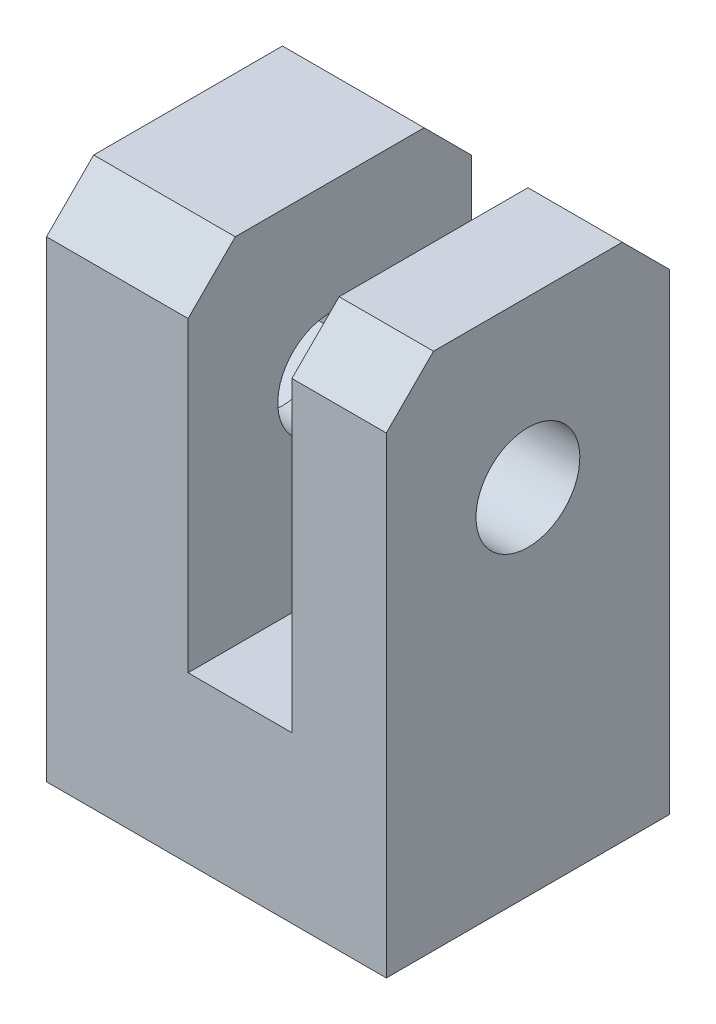
SolidWorks part; units mm, degrees
ref_plane "Front" through (0, 0, 0) normal (0, 0, 1) x (1, 0, 0)
ref_plane "Top" through (0, 0, 0) normal (0, 1, 0) x (1, 0, 0)
ref_plane "Right" through (0, 0, 0) normal (1, 0, 0) x (0, 0, -1)
sketch "Sketch1" plane through (0, 0, 0) normal (0, 0, 1) x (1, 0, 0)
  line L0 (-1.1, 7.5) -> (-1.1, 0)
  line L1 (-2.1, -3.5) -> (3.1, -3.5)
  line L2 (-2.1, -3.5) -> (-2.1, 7.5)
  line L3 (-2.1, 7.5) -> (3.1, 7.5) construction
  line L4 (3.1, -3.5) -> (3.1, 7.5)
  line L7 (-1.1, 0) -> (1.1, 0)
  line L8 (1.1, 0) -> (1.1, 7.5)
  line L10 (-2.1, 7.5) -> (-1.1, 7.5)
  line L11 (1.1, 7.5) -> (3.1, 7.5)
  point P0 (0, 0)
  dimension "D1" = 2
  dimension "D2" = 2.2
  dimension "D3" = 3.5
  dimension "D4" = 7.5
  dimension "D5" = 1
extrude "Boss-Extrude1" add sketch "Sketch1" along normal blind 6
sketch "Sketch2" plane through (1.1, 0, 0) normal (-1, 0, 0) x (0, 0, 1)
  line L0 (3, 4) -> (3, -3.5) construction
  line L2 (6, -3.5) -> (0, -3.5) construction
  circle A0 centre (3, 4) radius 1.1
  dimension "D1" = 2.2
  dimension "D2" = 7.5
extrude "Cut-Extrude1" cut sketch "Sketch2" against normal up to next
sketch "Sketch3" plane through (-1.1, 0, 0) normal (1, 0, 0) x (0, 0, -1)
  circle A0 centre (-3, 4) radius 1.1 construction
  circle A1 centre (-3, 4) radius 1.1
extrude "Cut-Extrude2" cut sketch "Sketch3" against normal up to next
sketch "Sketch5" plane through (-2.1, 0, 0) normal (-1, 0, 0) x (0, 0, 1)
  line L1 (5, 2.8453) -> (5, 5.1547)
  line L2 (5, 5.1547) -> (3, 6.3094)
  line L3 (3, 6.3094) -> (1, 5.1547)
  line L4 (0, 7.5) -> (0, -3.5)
  line L5 (0, -3.5) -> (6, -3.5)
  line L6 (6, -3.5) -> (6, 7.5)
  line L7 (6, 7.5) -> (0, 7.5)
  line L8 (0, 7.5) -> (0, -3.5)
  line L9 (0, -3.5) -> (6, -3.5)
  line L10 (6, -3.5) -> (6, 7.5)
  line L11 (6, 7.5) -> (0, 7.5)
  line L12 (1, 5.1547) -> (1, 2.8453)
  line L13 (1, 2.8453) -> (3, 1.6906)
  line L14 (3, 1.6906) -> (5, 2.8453)
  circle A0 centre (3, 4) radius 2 construction
  dimension "D2" = 4
  dimension "D1" = 0
extrude "Boss-Extrude2" add sketch "Sketch5" along normal blind 2
sketch "Sketch4" plane through (0, -3.5, 0) normal (0, -1, 0) x (1, 0, 0)
  line L0 (0, 0) -> (0, 6) construction
  line L1 (-4.1, 6) -> (3.1, 6) construction
  circle A0 centre (0, 3) radius 0.95
  dimension "D1" = 1.9
extrude "Cut-Extrude3" cut sketch "Sketch4" against normal up to next
chamfer "Chamfer1" distance 1 angle 45 4 edges at (-2.6, 7.5, 0) (2.1, 7.5, 0) (2.1, 7.5, 6) (-2.6, 7.5, 6)
